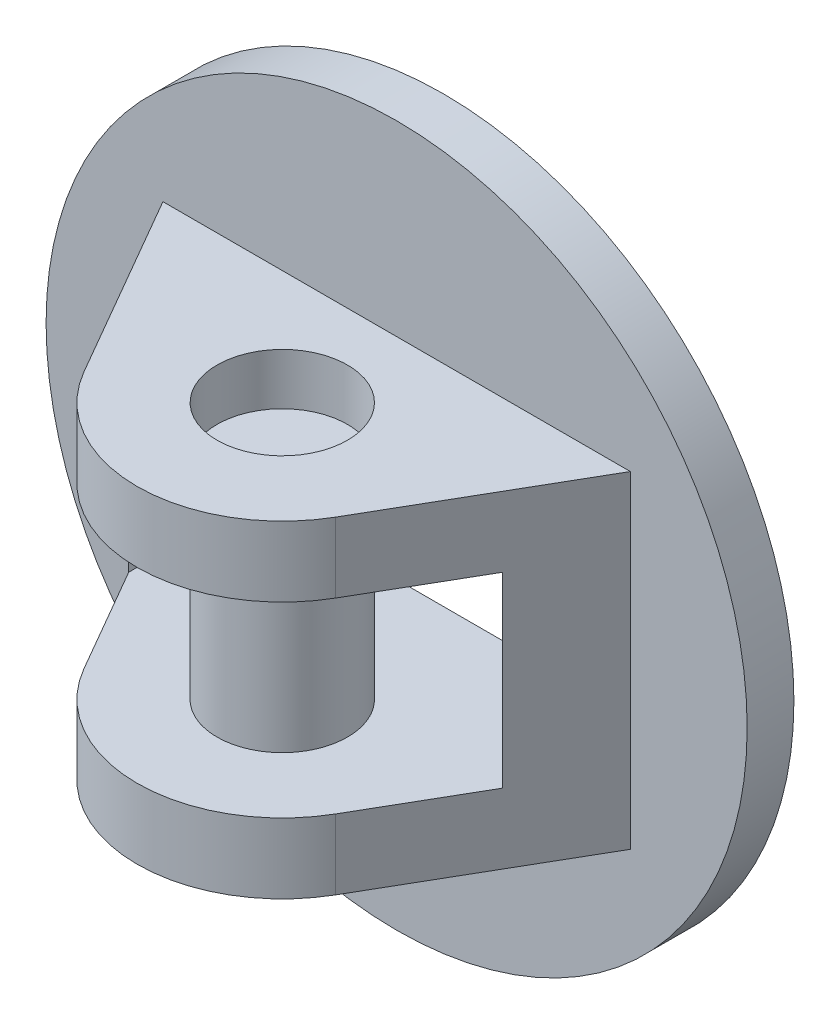
SolidWorks part; units mm, degrees
material "Chrome Stainless Steel"
ref_plane "Front Plane" through (0, 0, 0) normal (0, 0, 1) x (1, 0, 0)
ref_plane "Top Plane" through (0, 0, 0) normal (0, 1, 0) x (1, 0, 0)
ref_plane "Right Plane" through (0, 0, 0) normal (1, 0, 0) x (0, 0, -1)
other "Configuration Table"
sketch "Sketch2" plane through (0, 0, 0) normal (0, 0, 1) x (1, 0, 0)
  circle A0 centre (0, 0) radius 37.5
  dimension "D1" = 75
extrude "Extrude1" add sketch "Sketch2" along normal blind 5
sketch "Sketch4" plane through (0, 0, 0) normal (0, 1, 0) x (-1, 0, 0)
  line L0 (-25, 5) -> (25, 5)
  line L1 (37.5, 5) -> (-37.5, 5) construction
  line L2 (-25, 5) -> (-13.453, 25)
  line L3 (25, 5) -> (13.453, 25)
  arc A0 (-13.453, 25) -> (13.453, 25) centre (0, 17.2329) cw
  circle A1 centre (0, 17.2329) radius 6.9755
  dimension "D5" = 20
  dimension "D1" = 50
  dimension "D2" = 25
  dimension "D3" = 60
  dimension "D4" = 60
  dimension "D6" = 20
extrude "Extrude2" add sketch "Sketch4" along normal mid plane 35
ref_plane "Plane2" through (0, 0, 5) normal (0, 0, 1) x (1, 0, 0)
sketch "Sketch5" plane through (0, 0, 5) normal (0, 0, 1) x (1, 0, 0)
  line L1 (-20, 10) -> (20, 10)
  line L2 (-20, 10) -> (-20, -10)
  line L3 (-20, -10) -> (20, -10)
  line L4 (20, 10) -> (20, -10)
  line L7 (-13.453, -17.5) -> (13.453, -17.5) construction
  line L11 (25, 17.5) -> (25, -17.5) construction
  dimension "D1" = 20
  dimension "D2" = 7.5
  dimension "D3" = 40
  dimension "D4" = 5
extrude "Cut-Extrude3" cut sketch "Sketch5" against normal through all and the other way through all
sketch "Sketch6" plane through (0, -10, 0) normal (0, 1, 0) x (-1, 0, 0)
  circle A0 centre (0, 17.2329) radius 6.975
  dimension "D1" = 13.95
extrude "Extrude3" add sketch "Sketch6" along normal blind 22 and the other way blind 2
